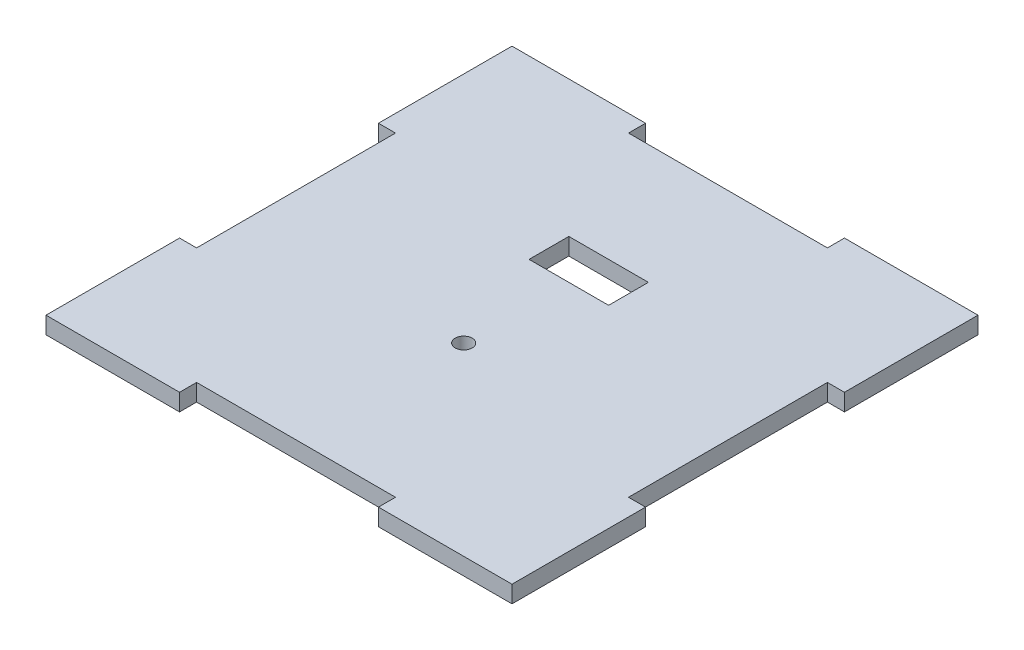
SolidWorks part; units mm, degrees
ref_plane "Front Plane" through (0, 0, 0) normal (0, 0, 1) x (1, 0, 0)
ref_plane "Top Plane" through (0, 0, 0) normal (0, 1, 0) x (1, 0, 0)
ref_plane "Right Plane" through (0, 0, 0) normal (1, 0, 0) x (0, 0, -1)
sketch "Sketch1" plane through (0, 0, 0) normal (0, 1, 0) x (1, 0, 0)
  line L0 (0, 38) -> (0, -38) construction
  line L1 (-41, -41) -> (-17.5, -41)
  line L2 (-41, -41) -> (-41, -17.5)
  line L3 (-41, 41) -> (-17.5, 41)
  line L4 (41, -41) -> (41, -17.5)
  line L5 (-41, -41) -> (41, 41) construction
  line L6 (-41, 41) -> (41, -41) construction
  line L11 (-41, 17.5) -> (-38, 17.5)
  line L12 (-38, 17.5) -> (-38, -17.5)
  line L13 (-35, 0) -> (38, 0) construction
  line L26 (17.5, 41) -> (41, 41)
  line L27 (41, 17.5) -> (41, 41)
  line L28 (17.5, -41) -> (41, -41)
  line L29 (-41, 17.5) -> (-41, 41)
  line L30 (-38, -17.5) -> (-41, -17.5)
  line L31 (-17.5, 41) -> (-17.5, 38)
  line L32 (-17.5, 38) -> (17.5, 38)
  line L33 (17.5, 38) -> (17.5, 41)
  line L34 (41, 17.5) -> (38, 17.5)
  line L35 (38, 17.5) -> (38, -17.5)
  line L36 (38, -17.5) -> (41, -17.5)
  line L37 (17.5, -41) -> (17.5, -38)
  line L38 (17.5, -38) -> (-17.5, -38)
  line L39 (-17.5, -38) -> (-17.5, -41)
  point P0 (0, 0)
  point P6 (0, 0)
  dimension "D1" = 3
  dimension "D2" = 82
  dimension "D3" = 3
  dimension "D4" = 82
  dimension "D5" = 3
  dimension "D6" = 3
extrude "Boss-Extrude1" add sketch "Sketch1" along normal blind 3
sketch "Sketch2" plane through (0, 3, 0) normal (0, 1, 0) x (1, 0, 0)
  line L1 (-7, 17) -> (7, 17)
  line L2 (-7, 17) -> (-7, 10)
  line L3 (-7, 10) -> (7, 10)
  line L4 (7, 17) -> (7, 10)
  line L5 (-7, 17) -> (7, 10) construction
  line L6 (-7, 10) -> (7, 17) construction
  circle A0 centre (0, -8.5) radius 1.5
  point P0 (0, 13.5)
  dimension "D3" = 3
  dimension "D1" = 14
  dimension "D2" = 7
  dimension "D4" = 8.5
  dimension "D5" = 13.5
  dimension "D6" = 0
extrude "Cut-Extrude1" cut sketch "Sketch2" against normal blind 3
